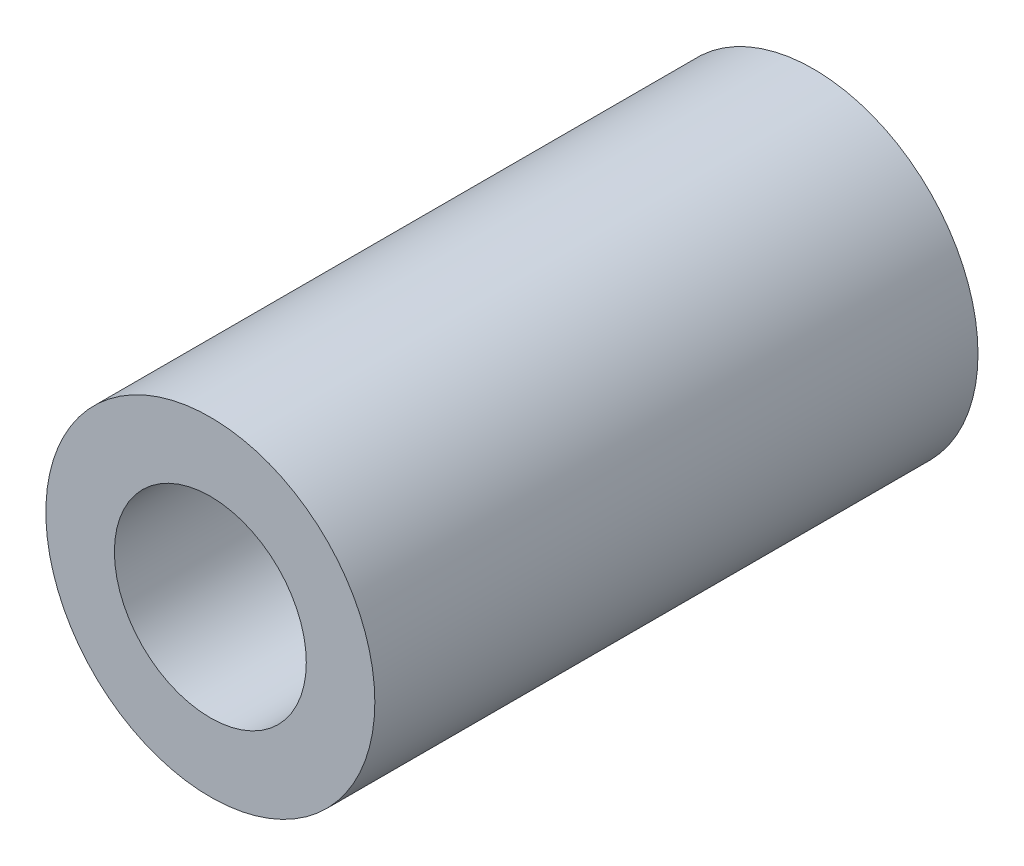
SolidWorks part; units mm, degrees
ref_plane "Front Plane" through (0, 0, 0) normal (0, 0, 1) x (1, 0, 0)
ref_plane "Top Plane" through (0, 0, 0) normal (0, 1, 0) x (1, 0, 0)
ref_plane "Right Plane" through (0, 0, 0) normal (1, 0, 0) x (0, 0, -1)
sketch "Sketch1" plane through (0, 0, 0) normal (0, 0, 1) x (1, 0, 0)
  circle A0 centre (0, 0) radius 3
  circle A1 centre (0, 0) radius 1.75
  dimension "D1" = 6
  dimension "D2" = 3.5
extrude "Boss-Extrude1" add sketch "Sketch1" along normal blind 11
